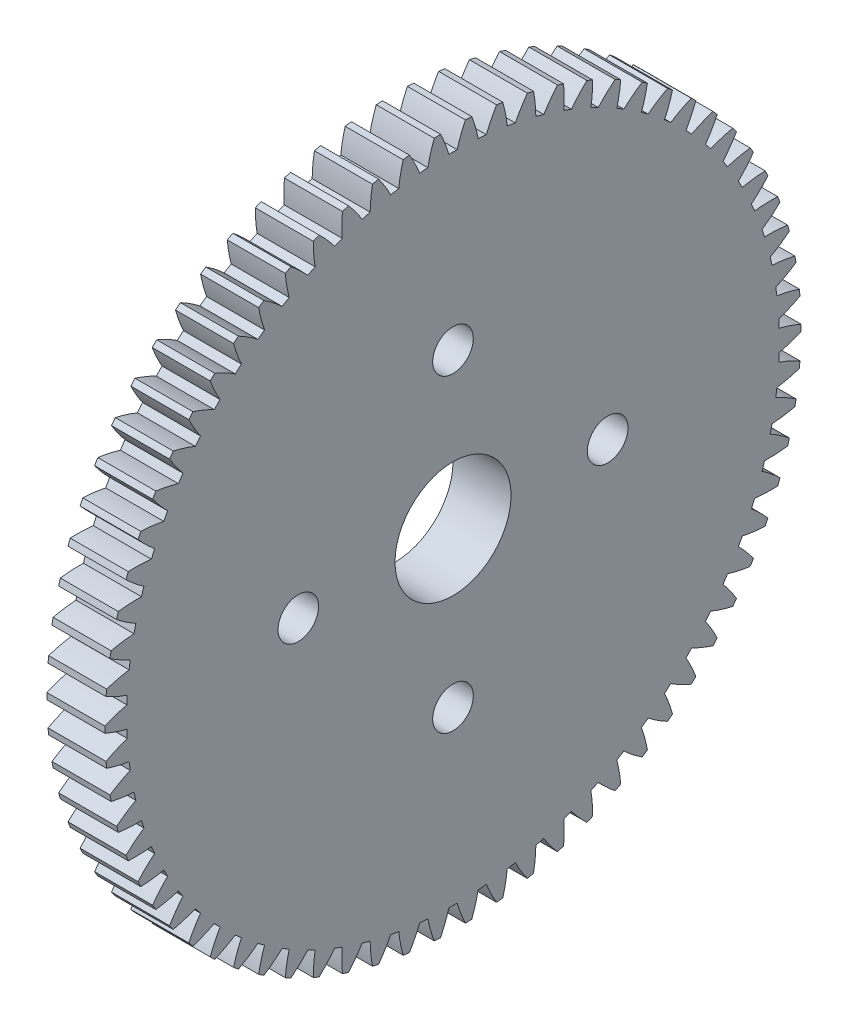
SolidWorks part; units mm, degrees
ref_plane "Plane1" through (0, 0, 0) normal (0, 0, 1) x (1, 0, 0)
ref_plane "Plane2" through (0, 0, 0) normal (0, 1, 0) x (1, 0, 0)
ref_plane "Plane3" through (0, 0, 0) normal (1, 0, 0) x (0, 0, -1)
sketch "HoldingSke" plane through (0, 0, 0) normal (0, 1, 0) x (1, 0, 0)
  line L0 (0, 0) -> (0.684, -1.8794)
  line L1 (-15, 0) -> (100, 0) construction
  line L2 (0, 0) -> (-2.1039, 2.3779)
  line L3 (0, 0) -> (-11.863, 4.5341)
  line L4 (0, 0) -> (2.9537, 8.1152)
  line L5 (0, 0) -> (-7.4956, -2.7956)
  line L6 (0, 0) -> (-2.4869, -1.6779)
  line L7 (-2.1039, 2.3779) -> (-0.3819, 10.1904)
  line L8 (-76.2, 54.61) -> (-75.2, 54.61)
  line L9 (-71.009, 38.7566) -> (-53.1078, 45.2721)
  line L10 (-76.2, 71.12) -> (104.1128, 71.12)
  line L11 (0, 0) -> (-3, 0)
  line L12 (-76.2, 101.6) -> (-76.181, 101.6)
  line L13 (24.9733, 27.94) -> (52.9518, 28.4284)
  line L14 (24.9733, 27.94) -> (24.9743, 27.94)
  line L15 (24.9733, 27.94) -> (100.4006, 29.5858)
  line L16 (-63.627, -0.5) -> (-12.827, -0.5)
  circle A0 centre (0, 0) radius 3
  circle A1 centre (0, 0) radius 7
  circle A2 centre (0, 0) radius 7
  circle A3 centre (0, 0) radius 3
  dimension "MHD" = 14
  dimension "Hub_dia" = 14
  dimension "Bore" = 6
  dimension "MBD" = 6
  dimension "Num_teeth" = 70
  dimension "Pitch" = 2
  dimension "Overall_len" = 8
  dimension "Show_teeth" = 70
  dimension "Thickness" = 3
  dimension "OAL" = 8.0001
  dimension "T_dim" = 1
  dimension "Ap" = 20
  dimension "H" = 19.05
  dimension "Pitch_radius" = 180.3128
  dimension "Width" = 3
  dimension "Backlash" = 0.019
  dimension "Addendum_fac" = 1
  dimension "Dedendum_fac" = 1.25
  dimension "Clearance_fac" = 0.25
  dimension "Dedendum_add" = 0.001
  dimension "Module" = 0.5
sketch "BasProSke" plane through (0, 0, 0) normal (0, 1, 0) x (1, 0, 0)
  line L0 (-10, 0) -> (60, 0) construction
  line L1 (0, 0) -> (0, 18)
  line L2 (0, 0) -> (3, 0)
  line L3 (3, 0) -> (3, 18)
  line L4 (3, 18) -> (0, 18)
  dimension "Thickness" = 3
  dimension "Diameter" = 36
revolve "Base-Revolve" add sketch "BasProSke" angle 360 about L0
sketch "TooCutSke" plane through (0, 0, 0) normal (1, 0, 0) x (0, 0, -1)
  line L1 (0, 0) -> (0, 107) construction
  line L2 (0, 0) -> (-0.4259, 17.4948) construction
  line L3 (0, 0) -> (-1.5699, 34.9574) construction
  line L4 (-0.4259, 17.4948) -> (-0.785, 17.4787) construction
  arc A0 (0.2122, 16.8727) -> (-0.2122, 16.8727) centre (0, 0) ccw
  arc A1 (0.6565, 18.0134) -> (-0.6565, 18.0134) centre (0, 0) ccw
  circle A2 centre (0, 0) radius 17.5 construction
  circle A3 centre (0, 0) radius 16.4446 construction
  arc A4 (-0.2122, 16.8727) -> (-0.6565, 18.0134) centre (-6.9321, 14.9121) ccw
  arc A5 (0.6565, 18.0134) -> (0.2122, 16.8727) centre (6.9321, 14.9121) ccw
  dimension "Root_dia" = 33.748
  dimension "Overcut_dia" = 36.0508
  dimension "Pitch_dia" = 35
  dimension "Base_dia" = 32.8892
  dimension "Flank_rad" = 7
  dimension "Half_ang" = 2.571
  dimension "Half_CT" = 0.3594
extrude "ToothCut" cut sketch "TooCutSke" along normal through all
fillet "Breaks" [suppressed] radius 0.01
fillet "RootFillets" [suppressed] radius 0.126
pattern_circular "TeethCuts" count 70 every 5.143 about axis through (-10, 0, 0) along (1, 0, 0) of "ToothCut", "RootFillets", "Breaks"
sketch "HubNeaOneSke" plane through (0, 0, 0) normal (-1, 0, 0) x (0, 0, 1)
  circle A0 centre (0, 0) radius 7
  dimension "Diameter" = 14
sketch "HubNeaBotSke" plane through (0, 0, 0) normal (-1, 0, 0) x (0, 0, 1)
  circle A0 centre (0, 0) radius 7
  dimension "Diameter" = 14
extrude "HubNearBoth" [suppressed] add sketch "HubNeaBotSke" along normal blind 2.5
ref_plane "FarPln" through (3, 0, 0) normal (1, 0, 0) x (0, 0, -1)
sketch "HubFarSke" plane through (3, 0, 0) normal (1, 0, 0) x (0, 0, -1)
  circle A0 centre (0, 0) radius 7
  dimension "Diameter" = 14
extrude "HubFar" [suppressed] add sketch "HubFarSke" along normal blind 2.5
sketch "BorSke" plane through (0, 0, 0) normal (1, 0, 0) x (0, 0, -1)
  circle A0 centre (0, 0) radius 3
  dimension "Diameter" = 6
extrude "Bore" cut sketch "BorSke" along normal mid plane 16.0001
sketch "KeySke" plane through (0, 0, 0) normal (1, 0, 0) x (0, 0, -1)
  line L0 (-1, 0) -> (-1, 4)
  line L1 (-1, 4) -> (1, 4)
  line L2 (1, 4) -> (1, 0)
  line L3 (0, 0) -> (0, 34) construction
  line L4 (-1, 0) -> (1, 0)
  dimension "Offset" = 4
  dimension "Width" = 2
extrude "Keyway" [suppressed] cut sketch "KeySke" along normal mid plane 16.0001
pattern_circular "Keyway2" [suppressed] count 2 every 90 about axis through (-10, 0, 0) along (1, 0, 0)
sketch "Sketch1" plane through (3, 0, 0) normal (1, 0, 0) x (0, 0, -1)
  circle A0 centre (0, 0) radius 8
  circle A1 centre (0, 8) radius 1.05
  circle A2 centre (8, 0) radius 1.05
  circle A3 centre (0, -8) radius 1.05
  circle A4 centre (-8, 0) radius 1.05
  point P14 (0, 0)
  dimension "D1" = 16
  dimension "D2" = 2.1
  dimension "D3" = 4
extrude "Cut-Extrude1" cut sketch "Sketch1" against normal blind 10 contours A4 | A2 | A3 | A1
sketch "Sketch3" plane through (0, 0, 0) normal (-1, 0, 0) x (0, 0, 1)
  circle A0 centre (0, 0) radius 14.5
  circle A1 centre (0, 0) radius 7.5
  dimension "D1" = 29
  dimension "D2" = 15
extrude "Cut-Extrude3" cut sketch "Sketch3" against normal blind 0.5
sketch "Sketch4" plane through (0.5, 0, 0) normal (-1, 0, 0) x (0, 0, 1)
  circle A0 centre (0, 0) radius 11 construction
  circle A1 centre (5.4948, 9.5293) radius 1.5
  circle A2 centre (9.5293, -5.4948) radius 1.5
  circle A3 centre (-5.4948, -9.5293) radius 1.5
  circle A4 centre (-9.5293, 5.4948) radius 1.5
  point P14 (0, 0)
  dimension "D1" = 22
  dimension "D2" = 3
  dimension "D3" = 4
extrude "Cut-Extrude4" [suppressed] cut sketch "Sketch4" against normal through all
equation "' \"Module@HoldingSke\" = 6.35"
equation "' \"Num_teeth@HoldingSke\" = 12"
equation "' \"Ap@HoldingSke\" =  20"
equation "' \"Ap@HoldingSke\" = 20"
equation "' \"Width@HoldingSke\" = 0.5 * 25.4"
equation "' \"Hub_dia@HoldingSke\"= 1 * 25.4"
equation "' \"Hub_dia@HoldingSke\" = 1 * 25.4"
equation "' \"Overall_len@HoldingSke\" = 1.0 * 25.4"
equation "' \"Bore@HoldingSke\" = 0.75 * 25.4"
equation "' \"T_dim@HoldingSke\" = 0.1 * 25.4"
equation "' \"Width@KeySke\" = 0.25 * 25.4"
equation "' \"Show_teeth@HoldingSke\" = 13"
equation "' \"Backlash@HoldingSke\" = 0.009 * 25.4"
equation "' \"Addendum_fac@HoldingSke\" = 1.0"
equation "' \"Dedendum_fac@HoldingSke\" = 1.25"
equation "' \"Dedendum_add@HoldingSke\" = 0.00005 * 25.4"
equation "' \"Clearance_fac@HoldingSke\" = 0.25"
equation "\"Pitch@HoldingSke\" = 1 / \"Module@HoldingSke\""
equation "\"Overcut_dia@TooCutSke\" = (\"Num_teeth@HoldingSke\" + 2 * \"Addendum_fac@HoldingSke\") / \"Pitch@HoldingSke\" + 0.002 * 25.4"
equation "\"Pitch_dia@TooCutSke\" = \"Num_teeth@HoldingSke\" / \"Pitch@HoldingSke\""
equation "\"Base_dia@TooCutSke\" = \"Num_teeth@HoldingSke\" / \"Pitch@HoldingSke\" * cos((\"Ap@HoldingSke\"  * 3.14159265 / 180))"
equation "\"Root_dia@TooCutSke\" = (\"Num_teeth@HoldingSke\" + 2) / \"Pitch@HoldingSke\" - 2 * (\"Addendum_fac@HoldingSke\" + \"Dedendum_fac@HoldingSke\") / \"Pitch@HoldingSke\" - \"Dedendum_add@HoldingSke\" * 2"
equation "\"Half_ang@TooCutSke\" = 180 / \"Num_teeth@HoldingSke\""
equation "\"Half_CT@TooCutSke\" = \"Num_teeth@HoldingSke\" / \"Pitch@HoldingSke\" * sin((3.14159265 / 2 / \"Num_teeth@HoldingSke\")) / 2 - 7 * \"Backlash@HoldingSke\" / 4"
equation "\"Flank_rad@TooCutSke\" = \"Num_teeth@HoldingSke\" / \"Pitch@HoldingSke\" / 5"
equation "\"Radius@RootFillets\" = \"Clearance_fac@HoldingSke\" / \"Pitch@HoldingSke\" + \"Dedendum_add@HoldingSke\""
equation "\"Break_rad@Breaks\" = 0.02 / \"Pitch@HoldingSke\""
equation "\"Thickness@HoldingSke\" = \"Width@HoldingSke\""
equation "\"OAL@HoldingSke\" = \"Thickness@HoldingSke\""
equation "\"MHD@HoldingSke\" = (\"Num_teeth@HoldingSke\" + 2) / \"Pitch@HoldingSke\" - 2 * (\"Addendum_fac@HoldingSke\" + \"Dedendum_fac@HoldingSke\")  / \"Pitch@HoldingSke\" - \"Dedendum_add@HoldingSke\" * 2"
equation "\"MBD@HoldingSke\" = (\"Num_teeth@HoldingSke\" + 2) / \"Pitch@HoldingSke\" - 2 * (\"Addendum_fac@HoldingSke\" + \"Dedendum_fac@HoldingSke\")  / \"Pitch@HoldingSke\" - \"Dedendum_add@HoldingSke\" * 2 - 0.002 * 25.4"
equation "\"MHD@HoldingSke\" = ((sgn( \"MHD@HoldingSke\" - \"Hub_dia@HoldingSke\" )-1)*( \"MHD@HoldingSke\" - \"Hub_dia@HoldingSke\" ))/-2+ \"Hub_dia@HoldingSke\""
equation "\"MBD@HoldingSke\" = ((sgn( \"MBD@HoldingSke\" - \"Bore@HoldingSke\" )-1)*( \"MBD@HoldingSke\" - \"Bore@HoldingSke\" ))/-2+ \"Bore@HoldingSke\""
equation "\"OAL@HoldingSke\" = ((sgn( \"OAL@HoldingSke\" - \"Overall_len@HoldingSke\" )+1)*( \"OAL@HoldingSke\" - \"Overall_len@HoldingSke\" ))/2 + \"Overall_len@HoldingSke\" + 0.000002 * 25.4"
equation "\"Num_teeth@TeethCuts\" = int( \"Show_teeth@HoldingSke\" ) + 1"
equation "\"Num_teeth@TeethCuts\" = ((sgn( \"Num_teeth@TeethCuts\" - \"Num_teeth@HoldingSke\" )-1)*( \"Num_teeth@TeethCuts\" - \"Num_teeth@HoldingSke\" ))/-2+ \"Num_teeth@HoldingSke\""
equation "\"Num_teeth@TeethCuts\" = ((sgn( \"Num_teeth@TeethCuts\" - 2.0)+1)*( \"Num_teeth@TeethCuts\" - 2.0))/2 +2.0"
equation "\"Angle@TeethCuts\" = 360.0 / \"Num_teeth@HoldingSke\""
equation "\"Diameter@BasProSke\" = (\"Num_teeth@HoldingSke\" + 2 * \"Addendum_fac@HoldingSke\") / \"Pitch@HoldingSke\""
equation "\"Thickness@BasProSke\"  = \"Thickness@HoldingSke\""
equation "' \"Fillet_rad@BasProSke\" =  \"Thickness@HoldingSke\" * 0.05"
equation "' \"Fillet_rad@BasProSke\" = \"Thickness@HoldingSke\" * 0.05"
equation "\"MHD@HoldingSke\" = ((sgn( \"MHD@HoldingSke\" - \"Root_dia@TooCutSke\" )-1)*( \"MHD@HoldingSke\" - \"Root_dia@TooCutSke\" ))/-2+ \"Root_dia@TooCutSke\""
equation "\"Diameter@HubNeaOneSke\" = \"MHD@HoldingSke\""
equation "\"Diameter@HubNeaBotSke\" = \"MHD@HoldingSke\""
equation "\"Length@HubNearBoth\" = ( \"OAL@HoldingSke\" - \"Thickness@BasProSke\" ) / 2.0"
equation "\"Thickness@FarPln\" = \"Thickness@BasProSke\""
equation "\"Diameter@HubFarSke\" = \"MHD@HoldingSke\""
equation "\"Length@HubFar\" = ( \"OAL@HoldingSke\" - \"Thickness@BasProSke\" ) / 2.0"
equation "\"Diameter@BorSke\" = \"MBD@HoldingSke\""
equation "\"D1@Bore\" = \"OAL@HoldingSke\" * 2.0"
equation "\"D1@Keyway\" = \"OAL@HoldingSke\" * 2.0"
equation "\"Offset@KeySke\" = \"T_dim@HoldingSke\" + \"MBD@HoldingSke\" / 2.0"
